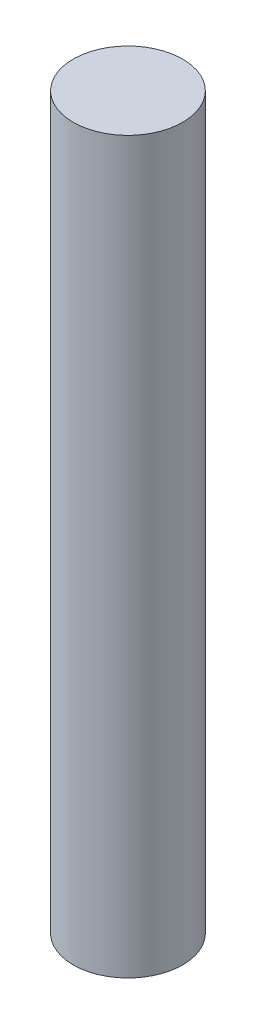
SolidWorks part; units mm, degrees
ref_plane "Front Plane" through (0, 0, 0) normal (0, 0, 1) x (1, 0, 0)
ref_plane "Top Plane" through (0, 0, 0) normal (0, 1, 0) x (1, 0, 0)
ref_plane "Right Plane" through (0, 0, 0) normal (1, 0, 0) x (0, 0, -1)
sketch "Sketch1" plane through (0, 0, 0) normal (0, 1, 0) x (1, 0, 0)
  circle A0 centre (0, 0) radius 3
  dimension "D1" = 6
extrude "Boss-Extrude1" add sketch "Sketch1" along normal blind 40
